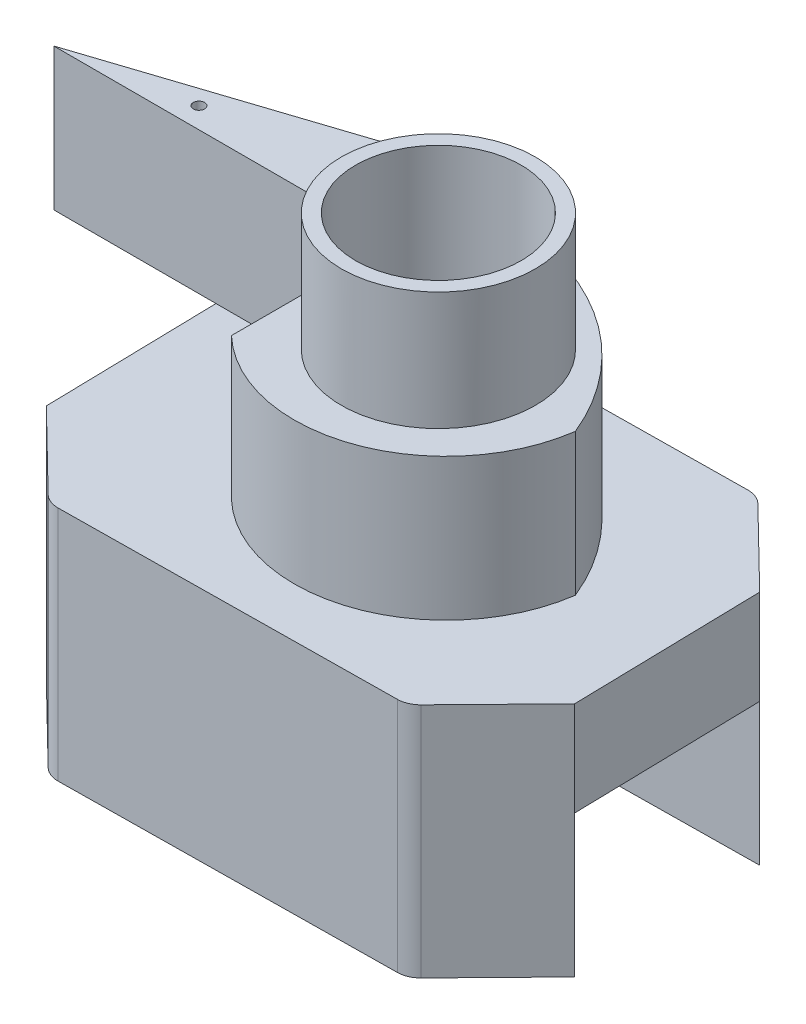
SolidWorks part; units mm, degrees
ref_plane "Front Plane" through (0, 0, 0) normal (0, 0, 1) x (1, 0, 0)
ref_plane "Top Plane" through (0, 0, 0) normal (0, 1, 0) x (1, 0, 0)
ref_plane "Right Plane" through (0, 0, 0) normal (1, 0, 0) x (0, 0, -1)
sketch "Sketch1" plane through (0, 0, 0) normal (0, 1, 0) x (1, 0, 0)
  line L1 (8.2124, 7.401) -> (-6.7876, 7.2242)
  line L2 (-6.7876, 7.2242) -> (-10.2812, 3.6472)
  line L3 (-10.2812, 3.6472) -> (-10.1044, -4.3528)
  line L4 (-10.1044, -4.3528) -> (-6.5274, -7.8464)
  line L5 (-6.5274, -7.8464) -> (8.4726, -7.6696)
  line L6 (8.4726, -7.6696) -> (11.9662, -4.0926)
  line L7 (11.9662, -4.0926) -> (11.7894, 3.9074)
  line L8 (11.7894, 3.9074) -> (8.2124, 7.401)
  dimension "D1" = 5
  dimension "D2" = 5
  dimension "D3" = 5
  dimension "D4" = 5
  dimension "D5" = 8
  dimension "D6" = 8
  dimension "D7" = 15
  dimension "D8" = 15
extrude "Boss-Extrude2" add sketch "Sketch1" along normal blind 10
sketch "Sketch4" plane through (0, 0, 0) normal (0, 1, 0) x (1, 0, 0)
  line L0 (-10.2812, 3.6472) -> (11.7894, 3.9074)
  line L1 (11.7894, 3.9074) -> (11.9662, -4.0926)
  line L2 (11.9662, -4.0926) -> (-10.1044, -4.3528)
  line L3 (-10.1044, -4.3528) -> (-10.2812, 3.6472)
extrude "Cut-Extrude2" cut sketch "Sketch4" along normal blind 6
ref_plane "secondfloor" through (0, 10, 0) normal (0, 1, 0) x (1, 0, 0)
sketch "Sketch5" plane through (0, 10, 0) normal (0, 1, 0) x (1, 0, 0)
  line L0 (-17.1216, 2.9808) -> (-4.0951, 7.2559)
  line L1 (8.2124, 7.401) -> (-6.7876, 7.2242) construction
  line L2 (-2.7662, -3.8668) -> (-2.7662, 2.9808)
  line L3 (-2.7662, 2.9808) -> (-17.1216, 2.9808)
  arc A0 (-4.0951, 7.2559) -> (-2.7662, 6.1515) centre (-3.7771, 6.2869) cw
  arc A2 (8.0087, -0.1019) -> (-2.7662, -3.8668) centre (1.6529, 0.7871) cw
  arc A3 (-2.7662, 6.1515) -> (8.0087, -0.1019) centre (-1.433, -3.961) cw
  dimension "D1" = 7.5
  dimension "D2" = 10.2
extrude "Boss-Extrude4" add sketch "Sketch5" along normal blind 6
ref_plane "3rdfloor" through (0, 16, 0) normal (0, 1, 0) x (1, 0, 0)
sketch "Sketch6" plane through (0, 16, 0) normal (0, 1, 0) x (1, 0, 0)
  circle A0 centre (2.1163, 0) radius 4.1
  dimension "D1" = 8.2
extrude "Boss-Extrude5" add sketch "Sketch6" along normal blind 5
ref_plane "Plane2" through (0, 21, 0) normal (0, 1, 0) x (1, 0, 0)
sketch "Sketch8" plane through (0, 21, 0) normal (0, 1, 0) x (1, 0, 0)
  circle A0 centre (2.1163, 0) radius 3.5
  circle A1 centre (2.1163, 0) radius 4.1 construction
  dimension "D1" = 0.6
extrude "Cut-Extrude3" cut sketch "Sketch8" against normal blind 15
sketch "Sketch9" plane through (0, 16, 0) normal (0, 1, 0) x (1, 0, 0)
  line L0 (-4.0951, 7.2559) -> (-17.1216, 2.9808) construction
  circle A0 centre (-11.8682, 3.8629) radius 0.2388
  dimension "D1" = 0.8
extrude "Cut-Extrude4" cut sketch "Sketch9" against normal blind 5
fillet "Fillet3" radius 1 1 edges at (8.4726, 5, 7.6696)
fillet "Fillet5" radius 1 3 edges at (-6.5274, 5, 7.8464) (-6.7876, 5, -7.2242) (8.2124, 5, -7.401)
